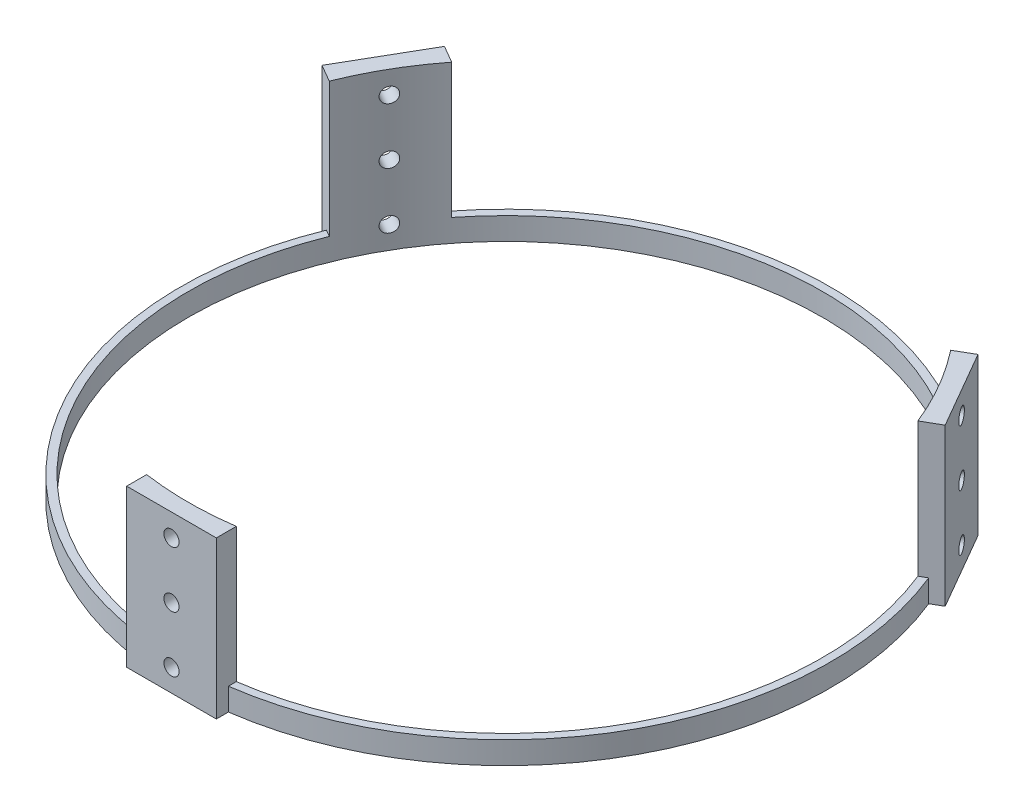
SolidWorks part; units mm, degrees
ref_plane "Front Plane" through (0, 0, 0) normal (0, 0, 1) x (1, 0, 0)
ref_plane "Top Plane" through (0, 0, 0) normal (0, 1, 0) x (1, 0, 0)
ref_plane "Right Plane" through (0, 0, 0) normal (1, 0, 0) x (0, 0, -1)
sketch "Sketch1" plane through (0, 0, 0) normal (0, 1, 0) x (1, 0, 0)
  circle A0 centre (0, 0) radius 92.075
  dimension "D2" = 184.15
extrude "Boss-Extrude1" add sketch "Sketch1" along normal blind 6.35
sketch "Sketch2" plane through (0, 0, 0) normal (0, 0, 1) x (1, 0, 0)
  line L1 (-12.7, 44.45) -> (12.7, 44.45)
  line L2 (-12.7, 44.45) -> (-12.7, 0)
  line L3 (-12.7, 0) -> (12.7, 0)
  line L4 (12.7, 44.45) -> (12.7, 0)
  line L5 (-12.7, 44.45) -> (12.7, 0) construction
  line L6 (-12.7, 0) -> (12.7, 44.45) construction
  point P0 (0, 22.225)
  point P5 (0, 0)
  dimension "D1" = 44.45
  dimension "D2" = 25.4
extrude "Boss-Extrude4" add sketch "Sketch2" against normal blind 6.35 from offset 94.615
sketch "Sketch4" plane through (0, 0, 94.615) normal (0, 0, 1) x (1, 0, 0)
  line L0 (-12.7, 0) -> (12.7, 0) construction
  line L1 (12.7, 44.45) -> (-12.7, 44.45) construction
  circle A0 centre (0, 38.1) radius 2.1463
  circle A1 centre (0, 22.225) radius 2.1463
  circle A2 centre (0, 6.35) radius 2.1463
  dimension "D1" = 4.2926
  dimension "D2" = 6.35
  dimension "D3" = 6.35
  dimension "D4" = 15.875
extrude "Cut-Extrude2" cut sketch "Sketch4" against normal blind 6.35
pattern_circular "CirPattern1" count 3 over 360 about axis through (0, 0, 0) along (0, 1, 0) of "Boss-Extrude4", "Cut-Extrude2"
sketch "Sketch3" plane through (0, 6.35, 0) normal (0, 1, 0) x (1, 0, 0)
  circle A0 centre (0, 0) radius 89.8525
  dimension "D1" = 179.705
extrude "Cut-Extrude1" cut sketch "Sketch3" against normal blind 6.35 and the other way blind 50.8
